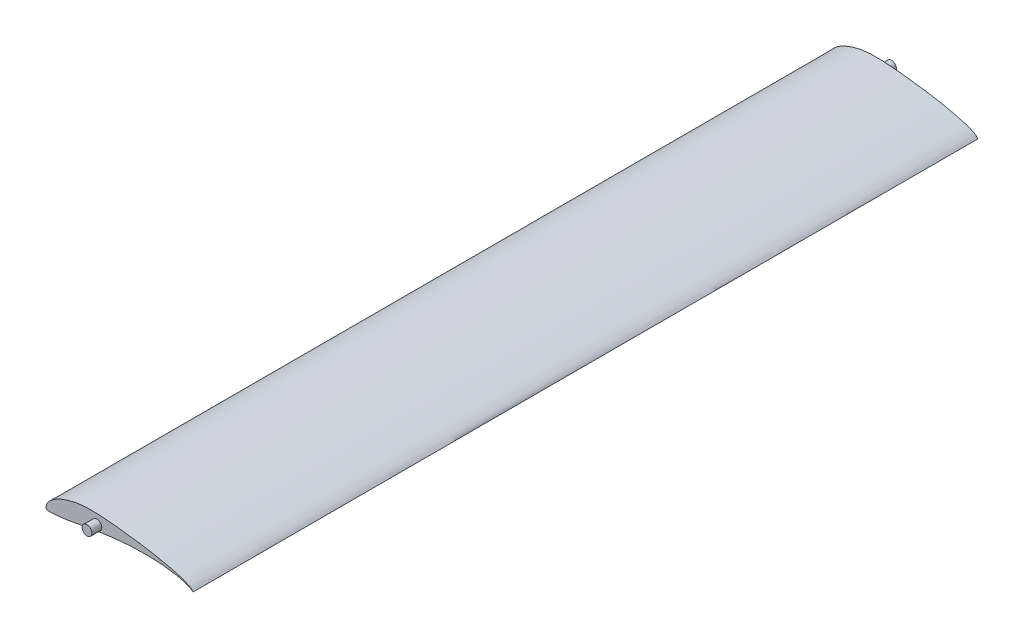
SolidWorks part; units mm, degrees
ref_plane "Front Plane" through (0, 0, 0) normal (0, 0, 1) x (1, 0, 0)
ref_plane "Top Plane" through (0, 0, 0) normal (0, 1, 0) x (1, 0, 0)
ref_plane "Right Plane" through (0, 0, 0) normal (1, 0, 0) x (0, 0, -1)
other "Center of Mass"
curve "Curve1"
  spline degree 3 poles (2530.1707, 6.596, 0) (2542.3026, -1.6396, 0) (2531.6653, 6.2859, 0) (2524.6036, 13.2147, 0) (2508.9237, 27.6868, 0) (2490.4252, 43.0823, 0) (2465.1208, 58.6027, 0) (2433.6545, 73.6437, 0) (2395.6673, 89.3408, 0) (2351.2171, 105.4755, 0) (2300.5113, 121.9337, 0) (2243.8131, 138.5726, 0) (2181.4399, 155.3141, 0) (2113.7362, 172.0044, 0) (2041.0902, 188.5227, 0) (1963.9348, 204.7659, 0) (1882.7412, 220.6505, 0) (1797.9839, 235.9809, 0) (1710.1966, 250.7353, 0) (1619.8853, 264.7237, 0) (1527.6341, 277.9734, 0) (1434.0341, 290.3794, 0) (1339.7632, 301.902, 0) (1245.5752, 312.6228, 0) (1152.2497, 322.2713, 0) (1060.5471, 330.6669, 0) (971.1123, 337.3371, 0) (884.4563, 341.9253, 0) (801.061, 343.9067, 0) (721.3537, 343.6958, 0) (645.4831, 339.7931, 0) (573.4199, 331.8844, 0) (504.8706, 320.7015, 0) (439.8187, 306.2141, 0) (378.3311, 289.2256, 0) (320.6679, 270.0368, 0) (267.0743, 249.0967, 0) (217.8834, 226.5172, 0) (173.253, 202.7568, 0) (133.4258, 178.0859, 0) (98.6515, 152.8385, 0) (68.9447, 127.55, 0) (44.736, 101.9442, 0) (26.1406, 76.2429, 0) (12.4047, 51.239, 0) (3.6014, 27.499, 0) (-0.5934, 5.5869, 0) (0.2163, -12.9455, 0) (4.9876, -29.9426, 0) (22.723, -38.3802, 0) (46.5686, -39.5639, 0) (79.1892, -40.7112, 0) (120.2119, -38.9423, 0) (169.1731, -35.6914, 0) (225.5279, -30.4842, 0) (288.6996, -23.4387, 0) (358.3802, -14.4036, 0) (434.5356, -1.7758, 0) (517.5367, 14.0593, 0) (607.7983, 31.293, 0) (704.8793, 49.4892, 0) (808.1699, 67.8929, 0) (916.9116, 85.8132, 0) (1030.2606, 102.6517, 0) (1147.2402, 117.7909, 0) (1266.7985, 130.7898, 0) (1387.806, 141.0649, 0) (1509.0483, 148.3486, 0) (1629.2589, 152.3529, 0) (1747.1336, 152.8587, 0) (1861.3574, 149.8316, 0) (1970.6224, 143.3424, 0) (2073.6145, 133.475, 0) (2169.1078, 120.608, 0) (2255.8588, 105.1149, 0) (2332.8504, 87.5144, 0) (2398.6638, 68.6812, 0) (2452.5253, 48.5807, 0) (2490.954, 30.1861, 0) (2519.2865, 13.1779, 0) (2530.1707, 6.596, 0) (2542.3026, -1.6396, 0) (2531.6653, 6.2859, 0) knots -0.009748 -0.004147 -0.001 0 0.00098 0.003649 0.007483 0.012095 0.017526 0.024052 0.031783 0.040678 0.05071 0.061833 0.073989 0.087118 0.101145 0.115991 0.13157 0.147788 0.164551 0.181758 0.199312 0.217095 0.23499 0.252857 0.270541 0.287887 0.304773 0.321101 0.336806 0.3518 0.366031 0.379616 0.392653 0.40517 0.417172 0.428604 0.439419 0.449597 0.459102 0.467908 0.475988 0.483309 0.489875 0.495803 0.501149 0.505903 0.510047 0.513579 0.516447 0.51935 0.523823 0.529974 0.537716 0.546968 0.557637 0.56962 0.582804 0.597247 0.613135 0.630444 0.649056 0.668822 0.689595 0.71119 0.733427 0.756094 0.778989 0.80189 0.824567 0.846792 0.868338 0.888978 0.908492 0.926659 0.943286 0.958169 0.971136 0.981956 0.990252 0.995853 0.999 1 1.00098 1.003649 1.007483 periodic
sketch "Sketch1" plane through (0, 0, 0) normal (0, 0, 1) x (1, 0, 0)
  line L0 (0, 0) -> (75, 0) construction
  line L1 (0, 0) -> (0, 14.0024) construction
  spline S1 degree 3 poles (74.7098, 0.1949) (75.068, -0.0484) (74.754, 0.1857) (74.5455, 0.3903) (74.0827, 0.8178) (73.5366, 1.2726) (72.7896, 1.7311) (71.8607, 2.1756) (70.7392, 2.6394) (69.4269, 3.1163) (67.9299, 3.6028) (66.2559, 4.0946) (64.4144, 4.5896) (62.4155, 5.0831) (60.2706, 5.5716) (57.9926, 6.052) (55.5954, 6.5218) (53.0929, 6.9753) (50.501, 7.4119) (47.8345, 7.8258) (45.1107, 8.218) (42.3471, 8.5853) (39.5637, 8.9265) (36.7827, 9.244) (34.0272, 9.5298) (31.3196, 9.7786) (28.6789, 9.9765) (26.1203, 10.1129) (23.6579, 10.1722) (21.3043, 10.1668) (19.0641, 10.0523) (16.9362, 9.8195) (14.912, 9.49) (12.9911, 9.0629) (11.1754, 8.5619) (9.4725, 7.9959) (7.8899, 7.3782) (6.4372, 6.712) (5.1191, 6.0109) (3.9429, 5.2828) (2.9159, 4.5377) (2.0385, 3.7913) (1.3234, 3.0355) (0.7741, 2.2768) (0.3682, 1.5386) (0.1081, 0.8377) (-0.016, 0.1908) (0.0077, -0.3564) (0.1484, -0.8583) (0.672, -1.1077) (1.3761, -1.1429) (2.3393, -1.1771) (3.5505, -1.1252) (4.9963, -1.0298) (6.6603, -0.8766) (8.5256, -0.6692) (10.5832, -0.4031) (12.832, -0.031) (15.2829, 0.4357) (17.9482, 0.9436) (20.8149, 1.4799) (23.865, 2.0223) (27.076, 2.5503) (30.423, 3.0463) (33.8772, 3.4922) (37.4075, 3.8748) (40.9806, 4.1769) (44.5606, 4.3908) (48.1101, 4.5078) (51.5906, 4.5215) (54.9633, 4.431) (58.1894, 4.2383) (61.2304, 3.9459) (64.0499, 3.565) (66.6112, 3.1066) (68.8844, 2.5861) (70.8275, 2.0294) (72.4176, 1.4353) (73.5521, 0.8918) (74.3885, 0.3893) (74.7098, 0.1949) (75.068, -0.0484) (74.754, 0.1857) knots -0.009748 -0.004147 -0.001 0 0.00098 0.003649 0.007483 0.012095 0.017526 0.024052 0.031783 0.040678 0.05071 0.061833 0.073989 0.087118 0.101145 0.115991 0.13157 0.147788 0.164551 0.181758 0.199312 0.217095 0.23499 0.252857 0.270541 0.287887 0.304773 0.321101 0.336806 0.3518 0.366031 0.379616 0.392653 0.40517 0.417172 0.428604 0.439419 0.449597 0.459102 0.467908 0.475988 0.483309 0.489875 0.495803 0.501149 0.505903 0.510047 0.513579 0.516447 0.51935 0.523823 0.529974 0.537716 0.546968 0.557637 0.56962 0.582804 0.597247 0.613135 0.630444 0.649056 0.668822 0.689595 0.71119 0.733427 0.756094 0.778989 0.80189 0.824567 0.846792 0.868338 0.888978 0.908492 0.926659 0.943286 0.958169 0.971136 0.981956 0.990252 0.995853 0.999 1 1.00098 1.003649 1.007483 only from (75, 0) to (75, 0)
  point P3 (246.2499, 0)
  point P5 (0, 14.0024)
  dimension "D1" = 75
extrude "Boss-Extrude1" add sketch "Sketch1" along normal mid plane 400
other "Center of Mass Reference Point1"
sketch "Sketch2" plane through (0, 0, 0) normal (0, 0, 1) x (1, 0, 0)
  circle A0 centre (25.9227, 5.1499) radius 2.5
  point P2 (20.085, 5.1251)
  dimension "D1" = 0
  dimension "D3" = 5
  dimension "D2" = 0
extrude "Boss-Extrude2" add sketch "Sketch2" along normal offset from surface (205 mm away) 5
mirror "Mirror1" about plane through (0, 0, 0) normal (0, 0, 1) of "Boss-Extrude2"
